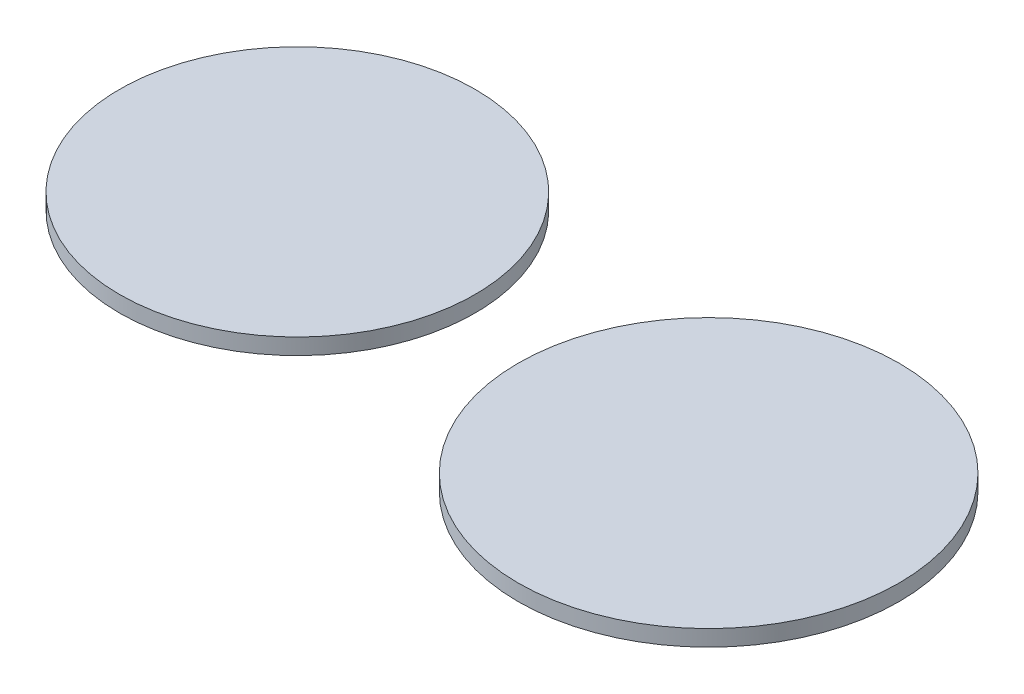
SolidWorks part; units mm, degrees
ref_plane "Front Plane" through (0, 0, 0) normal (0, 0, 1) x (1, 0, 0)
ref_plane "Top Plane" through (0, 0, 0) normal (0, 1, 0) x (1, 0, 0)
ref_plane "Right Plane" through (0, 0, 0) normal (1, 0, 0) x (0, 0, -1)
sketch "Sketch1" plane through (0, 0, 0) normal (0, 1, 0) x (1, 0, 0)
  circle A0 centre (0, 0) radius 30
  circle A1 centre (-70.7553, 5.9668) radius 28
extrude "Boss-Extrude1" add sketch "Sketch1" along normal blind 2.54
